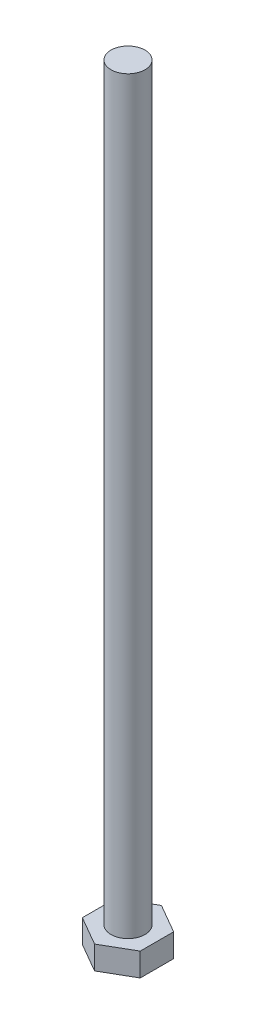
SolidWorks part; units mm, degrees
ref_plane "Спереди" through (0, 0, 0) normal (0, 0, 1) x (1, 0, 0)
ref_plane "Сверху" through (0, 0, 0) normal (0, 1, 0) x (1, 0, 0)
ref_plane "Справа" through (0, 0, 0) normal (1, 0, 0) x (0, 0, -1)
sketch "Эскиз1" plane through (0, 0, 0) normal (0, 1, 0) x (1, 0, 0)
  line L1 (8.5, -4.9075) -> (8.5, 4.9075)
  line L2 (8.5, 4.9075) -> (0, 9.815)
  line L3 (0, 9.815) -> (-8.5, 4.9075)
  line L4 (-8.5, 4.9075) -> (-8.5, -4.9075)
  line L5 (-8.5, -4.9075) -> (0, -9.815)
  line L6 (0, -9.815) -> (8.5, -4.9075)
  circle A0 centre (0, 0) radius 8.5 construction
extrude "Бобышка-Вытянуть1" add sketch "Эскиз1" along normal blind 8
sketch "Эскиз2" plane through (0, 8, 0) normal (0, 1, 0) x (1, 0, 0)
  circle A0 centre (0, 0) radius 5
extrude "Бобышка-Вытянуть2" add sketch "Эскиз2" along normal blind 220
chamfer "Фаска1" distance 2 angle 30 6 edges at (4.25, 0, -7.3612) (8.5, 0, 0) (4.25, 0, 7.3612) (-4.25, 0, 7.3612) (-8.5, 0, 0) (-4.25, 0, -7.3612)
